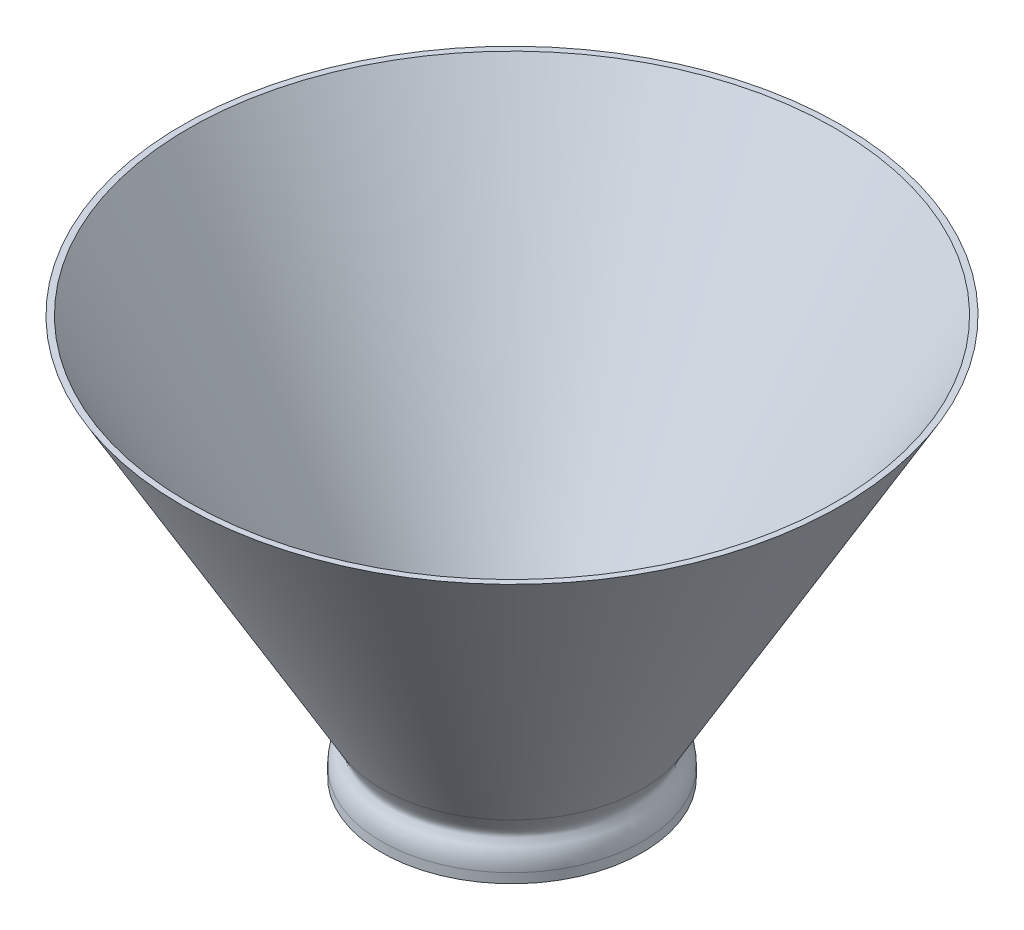
SolidWorks part; units mm, degrees
material "ABS"
ref_plane "Front Plane" through (0, 0, 0) normal (0, 0, 1) x (1, 0, 0)
ref_plane "Top Plane" through (0, 0, 0) normal (0, 1, 0) x (1, 0, 0)
ref_plane "Right Plane" through (0, 0, 0) normal (1, 0, 0) x (0, 0, -1)
sketch "Sketch1" plane through (0, 0, 0) normal (0, 0, 1) x (1, 0, 0)
  line L0 (0, 0) -> (0, 23755.1273) construction
  line L1 (0, 0) -> (23.25, 0) construction
  line L2 (23.25, 0) -> (81.25, 100.4589)
  line L3 (23.25, 0) -> (25, 0)
  line L4 (0, 0) -> (31.25, 0) construction
  line L5 (0, 0) -> (27, 0) construction
  line L6 (27, 0) -> (27, 3) construction
  line L7 (27, 3) -> (31.25, 3)
  line L8 (31.25, 3) -> (31.25, 0)
  line L9 (31.25, 0) -> (32.75, 0)
  line L10 (32.75, 0) -> (32.75, 13.8564) construction
  line L11 (32.75, 13.8564) -> (82.75, 100.4589)
  line L12 (82.75, 100.4589) -> (81.25, 100.4589)
  line L13 (27, 3) -> (25, 0)
  line L14 (32.75, 0) -> (32.75, 2.4)
  spline S0 degree 3 poles (32.75, 2.4) (32.75, 6.4081) (29.4828, 8.3393) (30.9235, 10.6928) (32.75, 13.8564) knots 0 0 0 0 0.53607 1 1 1 1
  dimension "D2" = 60
  dimension "D3" = 25
  dimension "D4" = 1.75
  dimension "D5" = 31.25
  dimension "D6" = 27
  dimension "D7" = 1.5
  dimension "D8" = 3
  dimension "D9" = 30.6
  dimension "D10" = 8.6
  dimension "D11" = 2.4
revolve "Revolve1" add sketch "Sketch1" angle 360 about L0
fillet "Fillet2" radius 1.5 2 edges at (0, 3, -27) (0, 3, -31.25)
sketch "Sketch2" plane through (0, 0, 0) normal (0, 1, 0) x (1, 0, 0)
  circle A0 centre (0, 0) radius 26.75
  dimension "D1" = 53.5
extrude "Cut-Extrude2" cut sketch "Sketch2" against normal through all and the other way through all contours A0
fillet "Fillet3" radius 10 1 edges at (0, 6.0622, 26.75)
sketch "Sketch3" plane through (0, 3, 0) normal (0, -1, 0) x (1, 0, 0)
  circle A0 centre (0, 0) radius 27.8028 construction
  circle A1 centre (0, 0) radius 27.8028
extrude "Cut-Extrude3" cut sketch "Sketch3" along normal through all
scale "Scale1" scale about centroid uniform scaling yes scale factor 1
scale "Scale2" scale about centroid uniform scaling yes scale factor 0.418779
